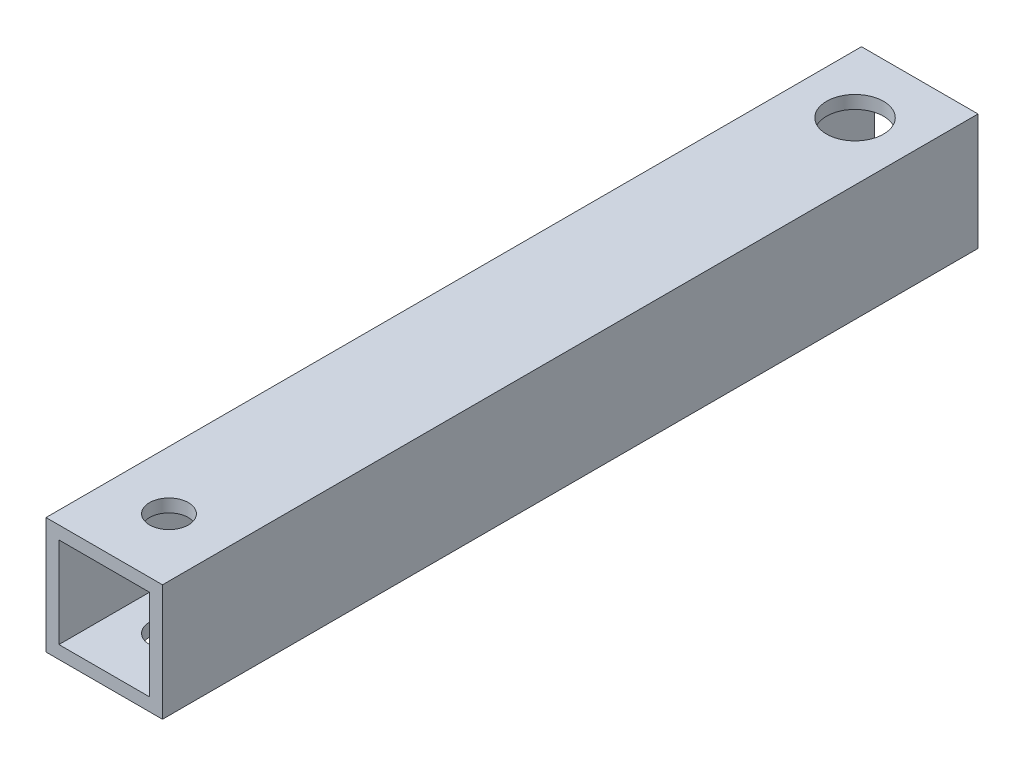
SolidWorks part; units mm, degrees
ref_plane "正面" through (0, 0, 0) normal (0, 0, 1) x (1, 0, 0)
ref_plane "平面" through (0, 0, 0) normal (0, 1, 0) x (1, 0, 0)
ref_plane "右側面" through (0, 0, 0) normal (1, 0, 0) x (0, 0, -1)
sketch "ｽｹｯﾁ1" plane through (0, 0, 0) normal (0, 0, 1) x (1, 0, 0)
  line L1 (-4.5, 4.5) -> (4.5, 4.5)
  line L2 (-4.5, 4.5) -> (-4.5, -4.5)
  line L3 (-4.5, -4.5) -> (4.5, -4.5)
  line L4 (4.5, 4.5) -> (4.5, -4.5)
  line L5 (-4.5, 4.5) -> (4.5, -4.5) construction
  line L6 (-4.5, -4.5) -> (4.5, 4.5) construction
  point P0 (0, 0)
  dimension "D1" = 9
  dimension "D2" = 9
extrude "ﾎﾞｽ - 押し出し1" add sketch "ｽｹｯﾁ1" along normal blind 63
sketch "ｽｹｯﾁ2" plane through (0, 0, 63) normal (0, 0, 1) x (1, 0, 0)
  line L1 (-3.5, 3.5) -> (3.5, 3.5)
  line L2 (-3.5, 3.5) -> (-3.5, -3.5)
  line L3 (-3.5, -3.5) -> (3.5, -3.5)
  line L4 (3.5, 3.5) -> (3.5, -3.5)
  line L5 (-3.5, 3.5) -> (3.5, -3.5) construction
  line L6 (-3.5, -3.5) -> (3.5, 3.5) construction
  point P0 (0, 0)
  dimension "D1" = 7
  dimension "D2" = 7
extrude "ｶｯﾄ - 押し出し1" cut sketch "ｽｹｯﾁ2" against normal blind 83
sketch "ｽｹｯﾁ3" plane through (0, 4.5, 0) normal (0, 1, 0) x (1, 0, 0)
  line L0 (0, 0) -> (0, -5)
  line L1 (0, -5) -> (0, -58)
  circle A0 centre (0, -5) radius 2.2
  circle A1 centre (0, -58) radius 1.5
  dimension "D1" = 4.4
  dimension "D2" = 3
  dimension "D3" = 5
  dimension "D4" = 53
extrude "ｶｯﾄ - 押し出し2" cut sketch "ｽｹｯﾁ3" against normal blind 93
